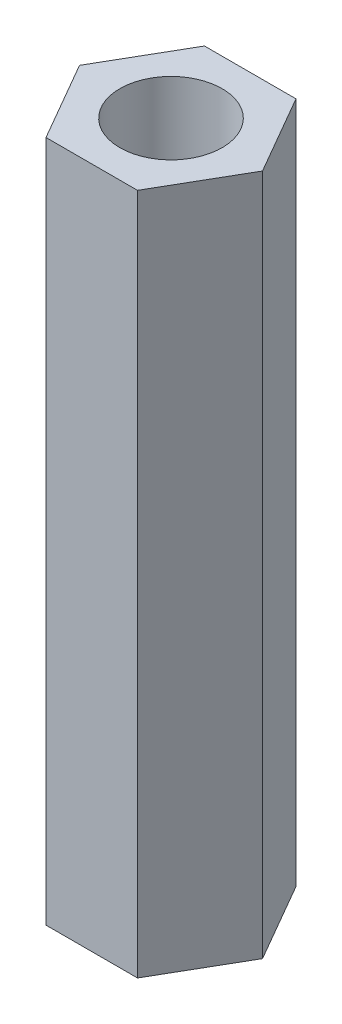
SolidWorks part; units mm, degrees
ref_plane "Front Plane" through (0, 0, 0) normal (0, 0, 1) x (1, 0, 0)
ref_plane "Top Plane" through (0, 0, 0) normal (0, 1, 0) x (1, 0, 0)
ref_plane "Right Plane" through (0, 0, 0) normal (1, 0, 0) x (0, 0, -1)
sketch "Sketch1" plane through (0, 0, 0) normal (0, 1, 0) x (1, 0, 0)
  line L0 (1.3414, 2.3233) -> (2.6828, 0)
  line L1 (-1.3414, 2.3233) -> (1.3414, 2.3233)
  line L2 (2.6828, 0) -> (1.3414, -2.3233)
  line L3 (1.3414, -2.3233) -> (-1.3414, -2.3233)
  line L4 (-1.3414, -2.3233) -> (-2.6828, 0)
  line L5 (-2.6828, 0) -> (-1.3414, 2.3233)
  circle A0 centre (0, 0) radius 1.5
  dimension "D1" = 3
  dimension "D3" = 6
extrude "Boss-Extrude1" add sketch "Sketch1" along normal blind 20
